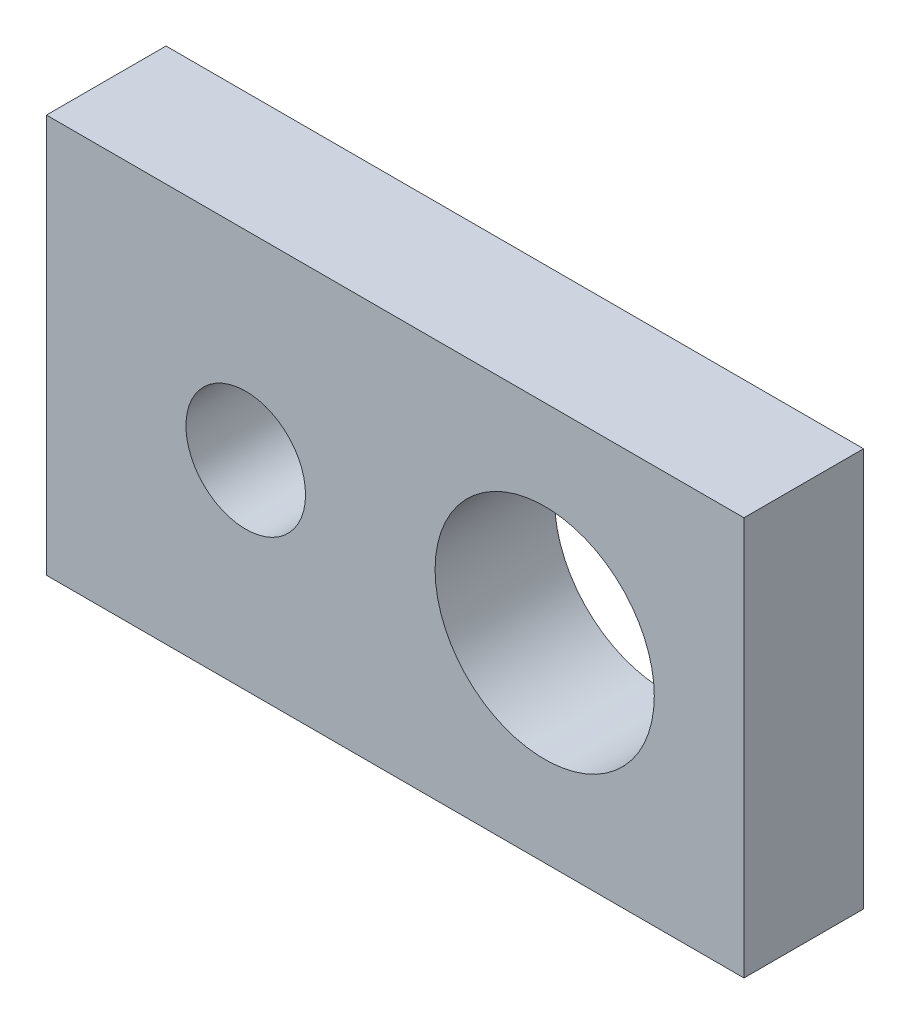
SolidWorks part; units mm, degrees
ref_plane "Front Plane" through (0, 0, 0) normal (0, 0, 1) x (1, 0, 0)
ref_plane "Top Plane" through (0, 0, 0) normal (0, 1, 0) x (1, 0, 0)
ref_plane "Right Plane" through (0, 0, 0) normal (1, 0, 0) x (0, 0, -1)
sketch "Sketch1" plane through (0, 0, 0) normal (0, 0, 1) x (1, 0, 0)
  line L0 (-7.5, 0) -> (7.5, 0)
  line L1 (-17.5, -10) -> (17.5, -10)
  line L2 (-17.5, -10) -> (-17.5, 10)
  line L3 (-17.5, 10) -> (17.5, 10)
  line L4 (17.5, -10) -> (17.5, 10)
  line L5 (-17.5, -10) -> (17.5, 10) construction
  line L6 (-17.5, 10) -> (17.5, -10) construction
  circle A0 centre (-7.5, 0) radius 3
  circle A1 centre (7.5, 0) radius 5.5
  point P0 (0, 0)
  point P9 (0, 0)
  dimension "D2" = 11
  dimension "D3" = 6
  dimension "D1" = 15
  dimension "D4" = 35
  dimension "D5" = 20
extrude "Boss-Extrude1" add sketch "Sketch1" along normal blind 6
